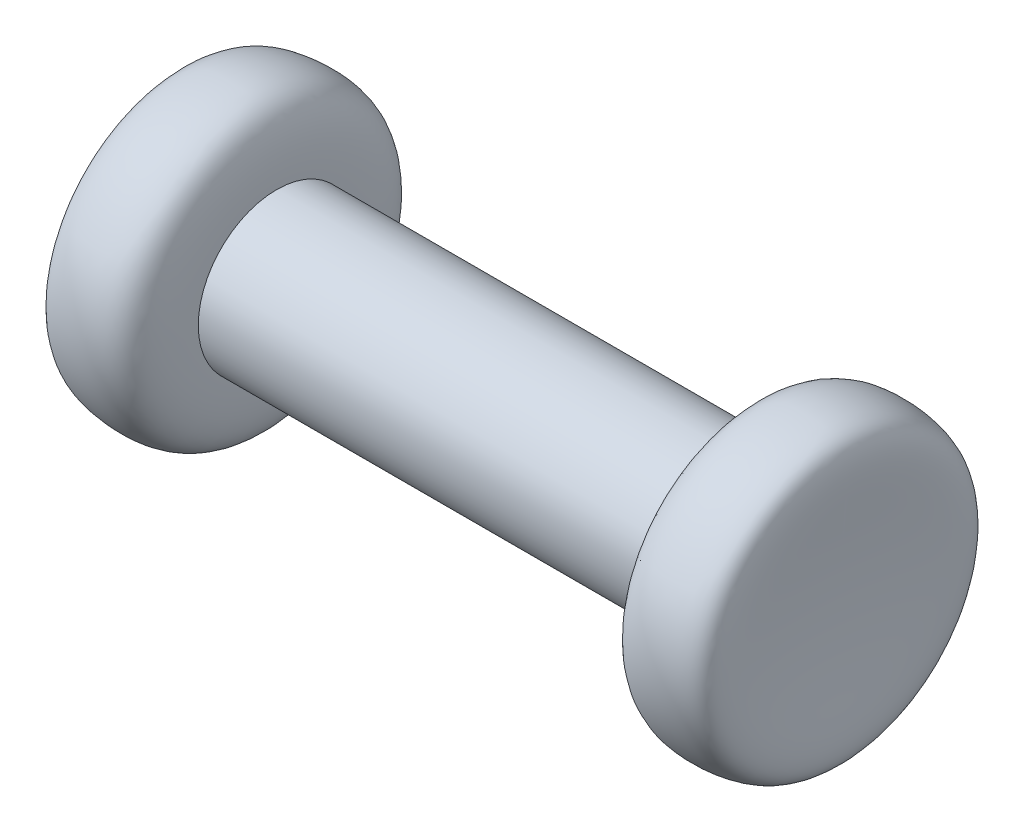
SolidWorks part; units mm, degrees
ref_plane "Front Plane" through (0, 0, 0) normal (0, 0, 1) x (1, 0, 0)
ref_plane "Top Plane" through (0, 0, 0) normal (0, 1, 0) x (1, 0, 0)
ref_plane "Right Plane" through (0, 0, 0) normal (1, 0, 0) x (0, 0, -1)
sketch "Sketch1" plane through (0, 0, 0) normal (0, 0, 1) x (1, 0, 0)
  line L0 (-7.5, 0) -> (7.5, 0)
  line L1 (0, 11.5712) -> (0, -19.9283) construction
  line L2 (7.5, 0) -> (7.5, 2.5) construction
  line L3 (7.5, 2.5) -> (10.5, 2.5) construction
  line L4 (10.5, 2.5) -> (10.5, -2.5) construction
  line L5 (10.5, -2.5) -> (-16.8911, -2.5) construction
  line L6 (-10.5, -2.5) -> (10.5, -2.5)
  spline S0 degree 3 poles (7.5, 0) (7.5, 1.2126) (7.7327, 2.3334) (11.3917, 2.1904) (10.5, 1.1336) (10.5, -2.5) knots 0 0 0 0 0.265537 0.444564 1 1 1 1
  spline S1 degree 3 poles (-7.5, 0) (-7.5, 1.2126) (-7.7327, 2.3334) (-11.3917, 2.1904) (-10.5, 1.1336) (-10.5, -2.5) knots 0 0 0 0 0.265537 0.444564 1 1 1 1
  point P5 (0, 0)
  dimension "D1" = 2.5
  dimension "D2" = 15
  dimension "D3" = 3
  dimension "D4" = 5
revolve "Revolve1" add sketch "Sketch1" angle 360 about L6
